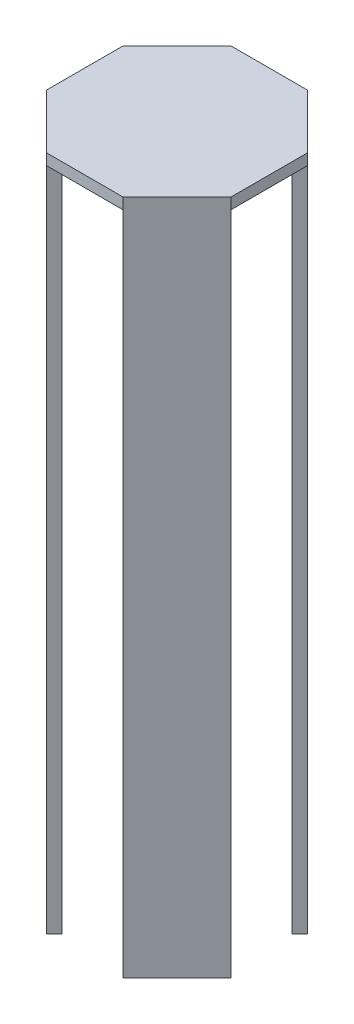
SolidWorks part; units mm, degrees
ref_plane "Plano frontal" through (0, 0, 0) normal (0, 0, 1) x (1, 0, 0)
ref_plane "Plano superior" through (0, 0, 0) normal (0, 1, 0) x (1, 0, 0)
ref_plane "Plano direito" through (0, 0, 0) normal (1, 0, 0) x (0, 0, -1)
sketch "Esboço1" plane through (0, 0, 0) normal (0, 1, 0) x (1, 0, 0)
  line L0 (10.3553, 25) -> (25, 10.3553) construction
  line L1 (10.3553, -25) -> (-10.3553, -25) construction
  line L2 (25, -10.3553) -> (25, 10.3553) construction
  line L3 (10.3553, 25) -> (-10.3553, 25) construction
  line L4 (-25, -10.3553) -> (-25, 10.3553) construction
  line L5 (-10.3553, -25) -> (10.3553, 25) construction
  line L6 (-10.3553, 25) -> (10.3553, -25) construction
  line L7 (25, -10.3553) -> (10.3553, -25) construction
  line L8 (-10.3553, -25) -> (-25, -10.3553) construction
  line L9 (-25, 10.3553) -> (-10.3553, 25) construction
  line L10 (0, 25) -> (0, -25) construction
  line L11 (-25, 0) -> (25, 0) construction
  line L12 (-25, 10.3553) -> (-10.3553, 25)
  line L13 (-10.3553, 25) -> (-8.234, 22.8787)
  line L14 (-8.234, 22.8787) -> (-22.8787, 8.234)
  line L15 (-22.8787, 8.234) -> (-25, 10.3553)
  line L16 (10.3553, 25) -> (25, 10.3553)
  line L17 (25, 10.3553) -> (22.8787, 8.234)
  line L18 (22.8787, 8.234) -> (8.234, 22.8787)
  line L19 (8.234, 22.8787) -> (10.3553, 25)
  line L20 (25, -10.3553) -> (10.3553, -25)
  line L21 (10.3553, -25) -> (8.234, -22.8787)
  line L22 (8.234, -22.8787) -> (22.8787, -8.234)
  line L23 (22.8787, -8.234) -> (25, -10.3553)
  line L24 (-10.3553, -25) -> (-25, -10.3553)
  line L25 (-25, -10.3553) -> (-22.8787, -8.234)
  line L26 (-22.8787, -8.234) -> (-8.234, -22.8787)
  line L27 (-8.234, -22.8787) -> (-10.3553, -25)
  point P0 (0, 0)
  point P19 (0, 0)
  point P20 (0, 0)
  point P33 (0, 0)
  dimension "D1" = 3
  dimension "D2" = 50
  dimension "D3" = 4
extrude "Ressalto-extrusão1" add sketch "Esboço1" along normal blind 180
sketch "Esboço2" plane through (0, 180, 0) normal (0, 1, 0) x (1, 0, 0)
  line L0 (-10.3553, 25) -> (10.3553, 25)
  line L1 (10.3553, 25) -> (25, 10.3553)
  line L2 (25, 10.3553) -> (25, -10.3553)
  line L3 (25, -10.3553) -> (10.3553, -25)
  line L4 (10.3553, -25) -> (-10.3553, -25)
  line L5 (-10.3553, -25) -> (-25, -10.3553)
  line L6 (-25, -10.3553) -> (-25, 10.3553)
  line L7 (-25, 10.3553) -> (-10.3553, 25)
extrude "Ressalto-extrusão2" add sketch "Esboço2" along normal blind 3
